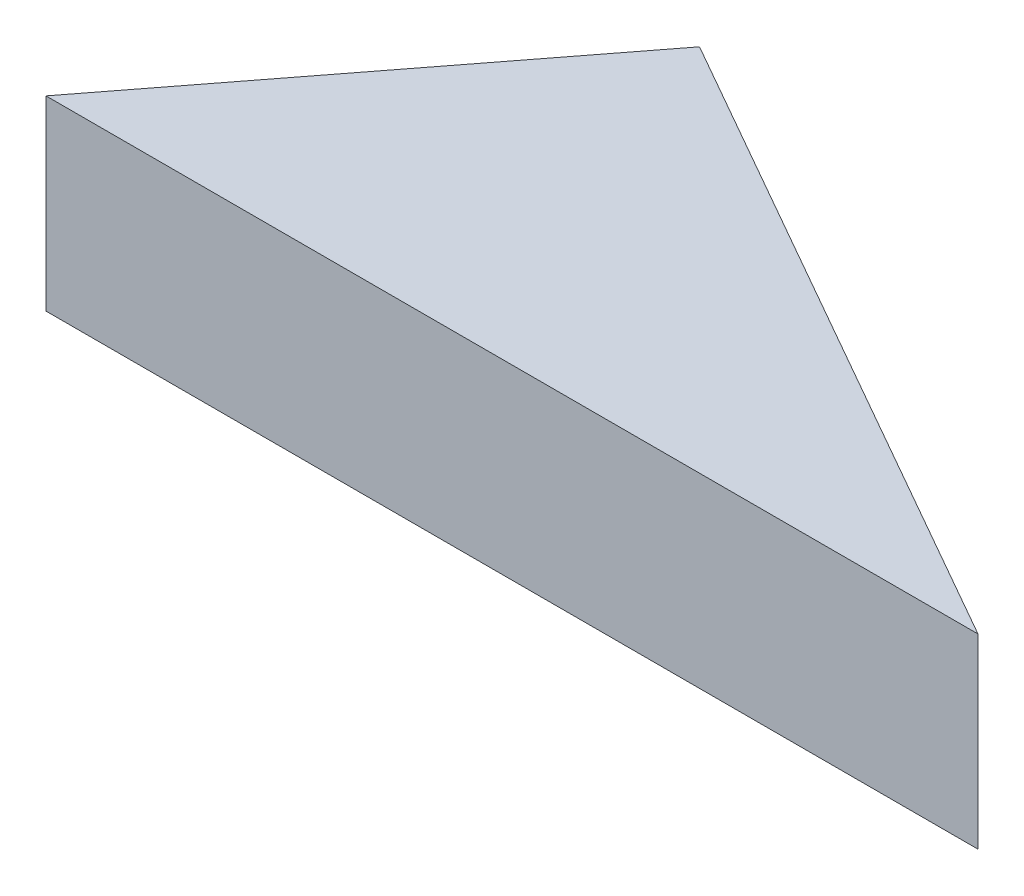
SolidWorks part; units mm, degrees
ref_plane "Front Plane" through (0, 0, 0) normal (0, 0, 1) x (1, 0, 0)
ref_plane "Top Plane" through (0, 0, 0) normal (0, 1, 0) x (1, 0, 0)
ref_plane "Right Plane" through (0, 0, 0) normal (1, 0, 0) x (0, 0, -1)
sketch "Sketch1" plane through (0, 0, 0) normal (0, 1, 0) x (1, 0, 0)
  line L0 (0, 0) -> (5, 0)
  line L1 (5, 0) -> (1.525, 1.981)
  line L2 (1.525, 1.981) -> (0, 0)
  dimension "D1" = 5
  dimension "D2" = 4
  dimension "D3" = 2.5
extrude "Boss-Extrude1" add sketch "Sketch1" along normal blind 1
equation "\"A\"= 5"
equation "\"D1@Sketch1\"=\"A\""
equation "\"B\"=4"
equation "\"D2@Sketch1\"=\"B\""
equation "\"D3@Sketch1\"=\"A\"/2"
equation "\"C\"= \"A\" - \"B\""
equation "\"D1@Boss-Extrude1\"=\"C\""
